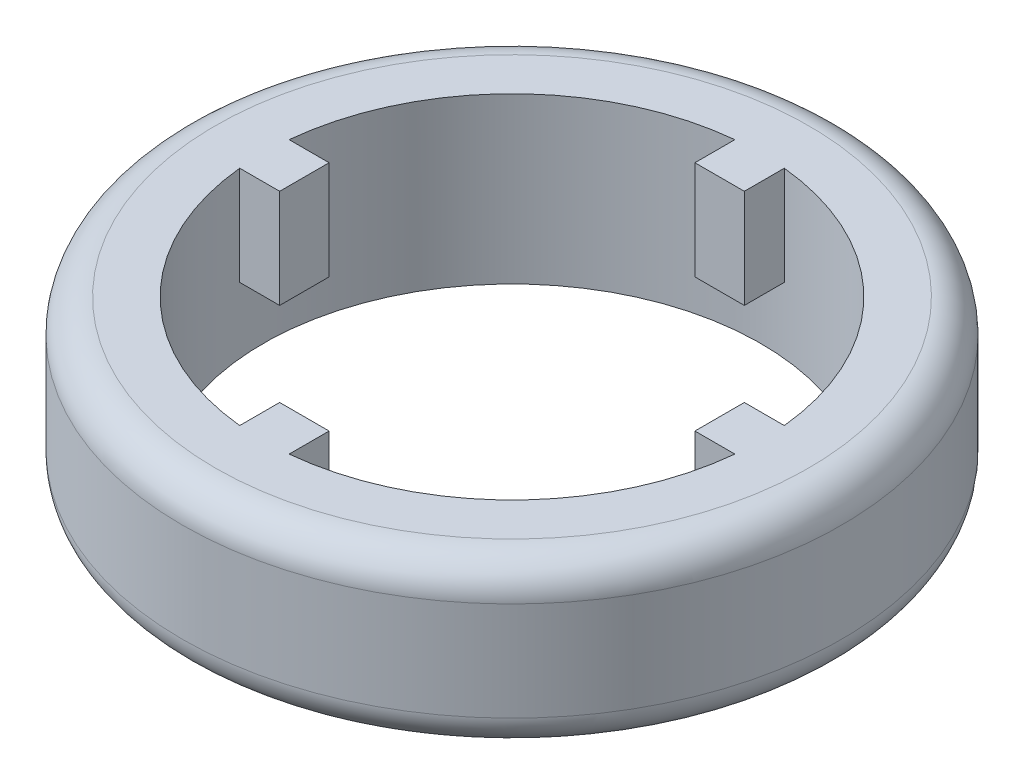
SolidWorks part; units mm, degrees
material "PET"
ref_plane "Спереди" through (0, 0, 0) normal (0, 0, 1) x (1, 0, 0)
ref_plane "Сверху" through (0, 0, 0) normal (0, 1, 0) x (1, 0, 0)
ref_plane "Справа" through (0, 0, 0) normal (1, 0, 0) x (0, 0, -1)
sketch "Эскиз1" plane through (0, 0, 0) normal (0, 1, 0) x (1, 0, 0)
  circle A0 centre (0, 0) radius 15.1
  circle A1 centre (0, 0) radius 20
  dimension "D1" = 30.2
  dimension "D2" = 40
extrude "Бобышка-Вытянуть1" add sketch "Эскиз1" along normal blind 10
fillet "Скругление1" radius 2 2 edges at (0, 10, 20) (0, 0, 20)
sketch "Эскиз2" plane through (0, 10, 0) normal (0, 1, 0) x (1, 0, 0)
  line L0 (0, 0) -> (-15.1, 0) construction
  line L1 (1.5, 12.6) -> (1.5, 17.6)
  line L2 (-12.6, 1.5) -> (-17.6, 1.5)
  line L3 (-12.6, 1.5) -> (-12.6, -1.5)
  line L4 (-12.6, -1.5) -> (-17.6, -1.5)
  line L5 (-17.6, 1.5) -> (-17.6, -1.5)
  line L6 (-12.6, 1.5) -> (-17.6, -1.5) construction
  line L7 (-12.6, -1.5) -> (-17.6, 1.5) construction
  line L8 (1.5, 12.6) -> (-1.5, 12.6)
  line L9 (-1.5, 12.6) -> (-1.5, 17.6)
  line L10 (1.5, 17.6) -> (-1.5, 17.6)
  line L11 (0, 0) -> (0, 15.1) construction
  line L12 (1.5, 12.6) -> (-1.5, 17.6) construction
  line L13 (-1.5, 12.6) -> (1.5, 17.6) construction
  line L14 (12.6, -1.5) -> (17.6, -1.5)
  line L15 (12.6, -1.5) -> (12.6, 1.5)
  line L16 (12.6, 1.5) -> (17.6, 1.5)
  line L17 (17.6, -1.5) -> (17.6, 1.5)
  line L18 (0, 0) -> (15.1, 0) construction
  line L19 (12.6, -1.5) -> (17.6, 1.5) construction
  line L20 (12.6, 1.5) -> (17.6, -1.5) construction
  line L21 (-1.5, -12.6) -> (-1.5, -17.6)
  line L22 (-1.5, -12.6) -> (1.5, -12.6)
  line L23 (1.5, -12.6) -> (1.5, -17.6)
  line L24 (-1.5, -17.6) -> (1.5, -17.6)
  line L25 (0, 0) -> (0, -15.1) construction
  line L26 (-1.5, -12.6) -> (1.5, -17.6) construction
  line L27 (1.5, -12.6) -> (-1.5, -17.6) construction
  circle A0 centre (0, 0) radius 15.1 construction
  point P28 (0, 0)
  dimension "D1" = 3
  dimension "D2" = 5
  dimension "D3" = 4
extrude "Бобышка-Вытянуть2" add sketch "Эскиз2" against normal blind 6
